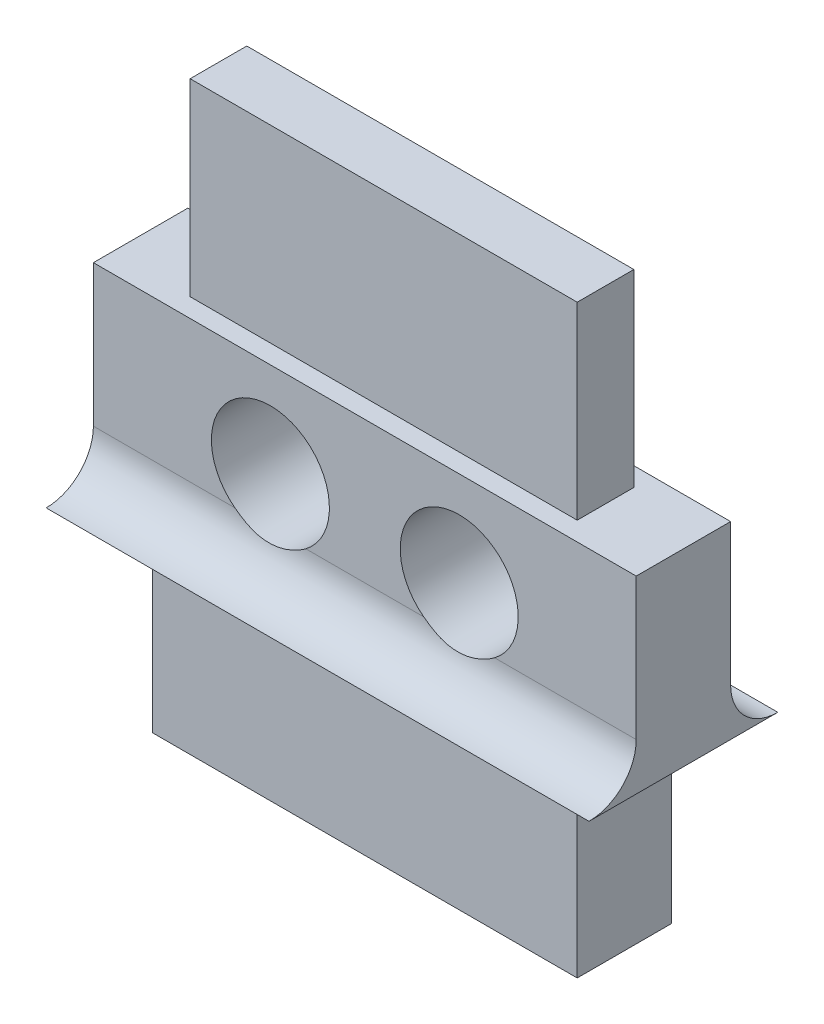
SolidWorks part; units mm, degrees
ref_plane "Front Plane" through (0, 0, 0) normal (0, 0, 1) x (1, 0, 0)
ref_plane "Top Plane" through (0, 0, 0) normal (0, 1, 0) x (1, 0, 0)
ref_plane "Right Plane" through (0, 0, 0) normal (1, 0, 0) x (0, 0, -1)
sketch "Model" plane through (0, 0, 0) normal (0, 0, 1) x (1, 0, 0)
  line L0 (5.7504, 12) -> (5.7504, 0) construction
  line L37 (1.25, 4) -> (0, 4)
  line L38 (10.2507, 4) -> (11.5007, 4)
  line L39 (1.25, 0) -> (10.2507, 0)
  line L40 (1.25, 4) -> (1.25, 0)
  line L41 (10.2507, 4) -> (10.2507, 0)
  line L126 (10.2507, 8) -> (11.5007, 8)
  line L127 (1.25, 8) -> (0, 8)
  line L128 (10.2507, 12) -> (1.25, 12)
  line L129 (10.2507, 8) -> (10.2507, 12)
  line L130 (1.25, 8) -> (1.25, 12)
  line L131 (0, 8) -> (0, 4)
  line L132 (11.5007, 8) -> (11.5007, 4)
  circle A81 centre (7.7507, 6) radius 1.25
  circle A82 centre (3.75, 6) radius 1.25
  dimension "D1" = 2.5
  dimension "D2" = 2
  dimension "D3" = 2.5
  dimension "D4" = 9.0007
  dimension "D5" = 4
  dimension "D6" = 2.5
extrude "Boss-Extrude1" add sketch "Model" along normal blind 2
sketch "Sketch1" plane through (0, 0, 0) normal (-1, 0, 0) x (0, 0, 1)
  line L0 (1, 0) -> (1, 7) construction
  line L1 (2, 4) -> (2, 5)
  line L2 (2, 4) -> (3, 4)
  line L3 (0, 4) -> (-1, 4)
  line L4 (0, 4) -> (0, 5)
  arc A0 (2, 5) -> (3, 4) centre (3, 5) ccw
  arc A1 (0, 5) -> (-1, 4) centre (-1, 5) cw
  dimension "D1" = 1
  dimension "D2" = 1
  dimension "D3" = 4
  dimension "D4" = 1
  dimension "D5" = 2
extrude "Boss-Extrude2" add sketch "Sketch1" against normal up to surface (11.5007 mm away) up to face at (11.5007, 6, 1)
sketch "Sketch2" plane through (0, 0, 2) normal (0, 0, 1) x (1, 0, 0)
  line L0 (5.7504, 12) -> (5.7504, 0) construction
  line L1 (10.2507, 12) -> (1.25, 12) construction
  line L2 (1.25, 0) -> (10.2507, 0) construction
  circle A0 centre (3.75, 6) radius 1.25
  circle A1 centre (7.7507, 6) radius 1.25
  dimension "D1" = 2.5
extrude "Cut-Extrude1" cut sketch "Sketch2" against normal through all both and the other way through all
sketch "Sketch3" plane through (0, 12, 0) normal (0, 1, 0) x (1, 0, 0)
  line L1 (10.2507, 0) -> (1.25, 0)
  line L2 (10.2507, 0) -> (10.2507, -2)
  line L3 (10.2507, -2) -> (1.25, -2)
  line L4 (1.25, 0) -> (1.25, -2)
  line L5 (9.8507, -0.4) -> (1.65, -0.4)
  line L6 (9.8507, -0.4) -> (9.8507, -1.6)
  line L7 (9.8507, -1.6) -> (1.65, -1.6)
  line L8 (1.65, -0.4) -> (1.65, -1.6)
  dimension "D1" = 0.4
  dimension "D2" = 0.4
  dimension "D3" = 0.4
  dimension "D4" = 0.4
extrude "Cut-Extrude2" cut sketch "Sketch3" against normal blind 4
equation "\"D4@Model\"= \"fingerWidth@parametersSketch@prostheticParameters.SLDPRT\" * 0.5556"
equation "\"D2@Sketch3\"=\"tol2@parametersSketch@prostheticParameters.SLDPRT\""
equation "\"D1@Sketch3\"=\"tol2@parametersSketch@prostheticParameters.SLDPRT\""
equation "\"D3@Sketch3\"=\"tol2@parametersSketch@prostheticParameters.SLDPRT\""
equation "\"D4@Sketch3\"=\"tol2@parametersSketch@prostheticParameters.SLDPRT\""
